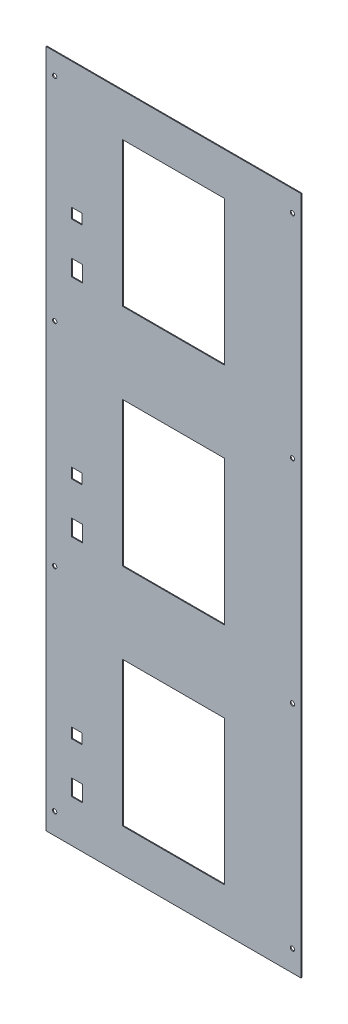
SolidWorks part; units mm, degrees
material "St.37"
ref_plane "Front Plane" through (0, 0, 0) normal (0, 0, 1) x (1, 0, 0)
ref_plane "Top Plane" through (0, 0, 0) normal (0, 1, 0) x (1, 0, 0)
ref_plane "Right Plane" through (0, 0, 0) normal (1, 0, 0) x (0, 0, -1)
sketch "Sketch1" plane through (0, 0, 0) normal (0, 0, 1) x (1, 0, 0)
  line L0 (-60, -85) -> (-60, 85)
  line L1 (-150, -400) -> (150, -400)
  line L2 (-150, -400) -> (-150, 400)
  line L3 (-150, 400) -> (150, 400)
  line L4 (150, -400) -> (150, 400)
  line L5 (-150, -400) -> (150, 400) construction
  line L6 (-150, 400) -> (150, -400) construction
  line L7 (-60, 180) -> (60, 180)
  line L8 (-60, 180) -> (-60, 350)
  line L9 (-60, 350) -> (60, 350)
  line L10 (60, 180) -> (60, 350)
  line L11 (-60, 180) -> (60, 350) construction
  line L12 (-60, 350) -> (60, 180) construction
  line L13 (-60, -85) -> (60, -85)
  line L14 (60, -85) -> (60, 85)
  line L15 (-60, 85) -> (60, 85)
  line L16 (-60, -350) -> (-60, -180)
  line L17 (-60, -350) -> (60, -350)
  line L18 (60, -350) -> (60, -180)
  line L19 (-60, -180) -> (60, -180)
  point P0 (0, 0)
  point P6 (0, 265)
  dimension "D1" = 300
  dimension "D2" = 800
  dimension "D3" = 120
  dimension "D4" = 150
  dimension "D5" = 170
  dimension "D6" = 50
  dimension "D8" = 50
  dimension "D7" = 3
extrude "Boss-Extrude1" add sketch "Sketch1" along normal blind 1
sketch "Sketch4" plane through (0, 0, 1) normal (0, 0, 1) x (1, 0, 0)
  line L0 (150, 400) -> (-150, 400) construction
  line L1 (150, -400) -> (150, 400) construction
  line L2 (-150, -400) -> (150, -400) construction
  line L3 (-150, 400) -> (-150, -400) construction
  circle A0 centre (140, 375) radius 2.5
  circle A2 centre (-140, 375) radius 2.5
  circle A3 centre (-140, 125) radius 2.5
  circle A4 centre (-140, -125) radius 2.5
  circle A5 centre (-140, -375) radius 2.5
  circle A8 centre (140, 125) radius 2.5
  circle A9 centre (140, -125) radius 2.5
  circle A10 centre (140, -375) radius 2.5
  dimension "D1" = 25
  dimension "D4" = 25
  dimension "D8" = 5
  dimension "D3" = 10
  dimension "D5" = 10
  dimension "D6" = 10
  dimension "D7" = 2
  dimension "D2" = 4
extrude "Cut-Extrude1" cut sketch "Sketch4" against normal blind 10
sketch "Sketch5" plane through (0, 0, 1) normal (0, 0, 1) x (1, 0, 0)
  line L0 (-150, 400) -> (-150, -400) construction
  line L1 (-107.4, 199) -> (-120, 199)
  line L2 (-107.4, 199) -> (-107.4, 180)
  line L3 (-107.4, 180) -> (-120, 180)
  line L4 (-120, 199) -> (-120, 180)
  line L5 (-107.4, 199) -> (-120, 180) construction
  line L6 (-107.4, 180) -> (-120, 199) construction
  line L8 (-107.4, -66) -> (-107.4, -85)
  line L9 (-107.4, -66) -> (-120, -66)
  line L10 (-120, -66) -> (-120, -85)
  line L11 (-107.4, -85) -> (-120, -85)
  line L12 (-107.4, -331) -> (-107.4, -350)
  line L13 (-107.4, -331) -> (-120, -331)
  line L14 (-120, -331) -> (-120, -350)
  line L15 (-107.4, -350) -> (-120, -350)
  line L17 (-108, -14) -> (-108, -26)
  line L18 (-108, 251) -> (-120, 251)
  line L19 (-108, 251) -> (-108, 239)
  line L20 (-108, 239) -> (-120, 239)
  line L21 (-120, 251) -> (-120, 239)
  line L22 (-108, 251) -> (-120, 239) construction
  line L23 (-108, 239) -> (-120, 251) construction
  line L24 (-108, -14) -> (-120, -14)
  line L25 (-120, -14) -> (-120, -26)
  line L26 (-108, -26) -> (-120, -26)
  line L27 (-108, -279) -> (-108, -291)
  line L28 (-108, -279) -> (-120, -279)
  line L29 (-120, -279) -> (-120, -291)
  line L30 (-108, -291) -> (-120, -291)
  line L31 (-150, -400) -> (150, -400) construction
  point P0 (-113.7, 189.5)
  point P9 (-114, 245)
  dimension "D1" = 12.6
  dimension "D2" = 19
  dimension "D3" = 30
  dimension "D4" = 50
  dimension "D6" = 265
  dimension "D7" = 12
  dimension "D8" = 12
  dimension "D9" = 30
  dimension "D10" = 40
  dimension "D12" = 265
  dimension "D5" = 3
  dimension "D11" = 3
extrude "Cut-Extrude2" cut sketch "Sketch5" against normal blind 10
